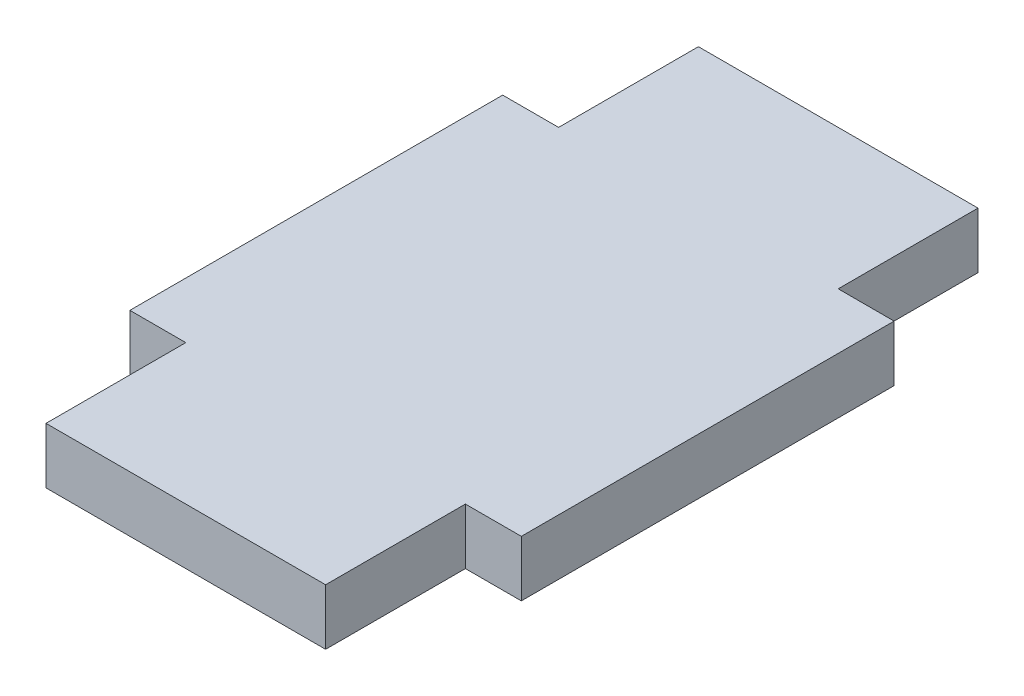
SolidWorks part; units mm, degrees
ref_plane "Front Plane" through (0, 0, 0) normal (0, 0, 1) x (1, 0, 0)
ref_plane "Top Plane" through (0, 0, 0) normal (0, 1, 0) x (1, 0, 0)
ref_plane "Right Plane" through (0, 0, 0) normal (1, 0, 0) x (0, 0, -1)
sketch "Sketch2" plane through (0, 0, 0) normal (0, 1, 0) x (1, 0, 0)
  line L0 (-10.5, 10) -> (-7.5, 10)
  line L1 (-7.5, 10) -> (-7.5, 17.5)
  line L2 (-7.5, 17.5) -> (7.5, 17.5)
  line L3 (7.5, 17.5) -> (7.5, 10)
  line L4 (7.5, 10) -> (10.5, 10)
  line L5 (10.5, 10) -> (10.5, -10)
  line L6 (10.5, -10) -> (7.5, -10)
  line L7 (7.5, -10) -> (7.5, -17.5)
  line L8 (7.5, -17.5) -> (-7.5, -17.5)
  line L9 (-7.5, -17.5) -> (-7.5, -10)
  line L10 (-7.5, -10) -> (-10.5, -10)
  line L11 (-10.5, -10) -> (-10.5, 10)
  point P11 (0, 17.5)
  point P13 (10.5, 0)
  dimension "D1" = 20
  dimension "D2" = 35
  dimension "D3" = 3
  dimension "D4" = 15
extrude "Boss-Extrude1" add sketch "Sketch2" along normal mid plane 3
